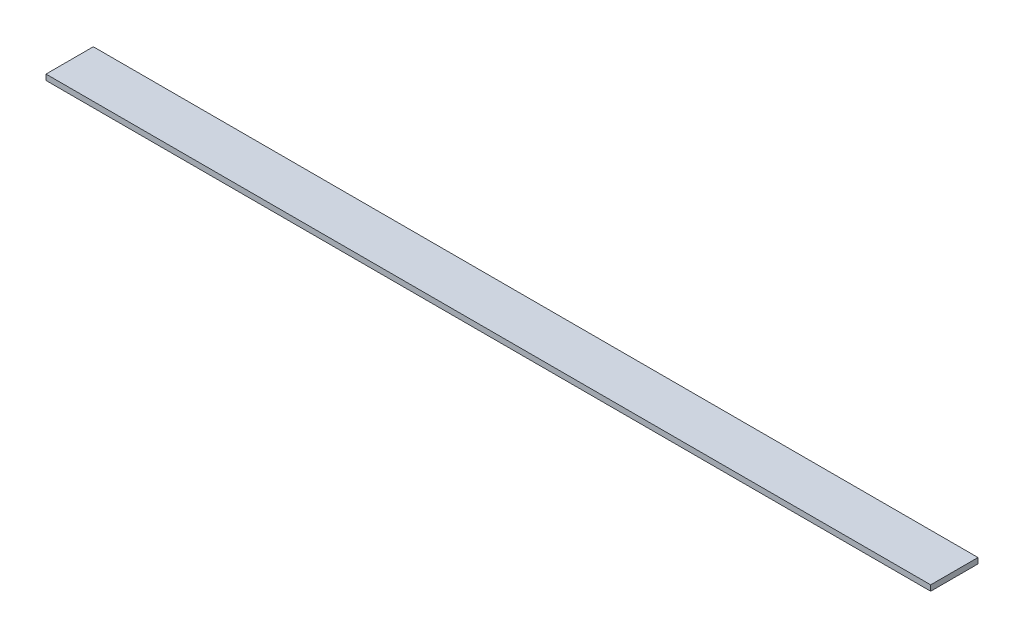
SolidWorks part; units mm, degrees
material "6061 Alloy"
ref_plane "Front Plane" through (0, 0, 0) normal (0, 0, 1) x (1, 0, 0)
ref_plane "Top Plane" through (0, 0, 0) normal (0, 1, 0) x (1, 0, 0)
ref_plane "Right Plane" through (0, 0, 0) normal (1, 0, 0) x (0, 0, -1)
sketch "Sketch1" plane through (0, 334.9257, 0) normal (0, 1, 0) x (1, 0, 0)
  line L1 (32.8749, 70.7173) -> (507.7249, 70.7173)
  line L2 (32.8749, 70.7173) -> (32.8749, 45.3173)
  line L3 (32.8749, 45.3173) -> (507.7249, 45.3173)
  line L4 (507.7249, 70.7173) -> (507.7249, 45.3173)
  line L5 (0.2999, 45.3173) -> (540.2999, 45.3173) construction
  line L7 (507.7249, 45.3173) -> (507.7249, 70.7173) construction
  line L8 (507.7249, 70.7173) -> (32.8749, 70.7173) construction
  point P5 (0, 0)
  point P6 (0, 0)
  point P9 (0, 0)
  point P12 (0, 0)
extrude "Boss-Extrude1" add sketch "Sketch1" along normal blind 3
